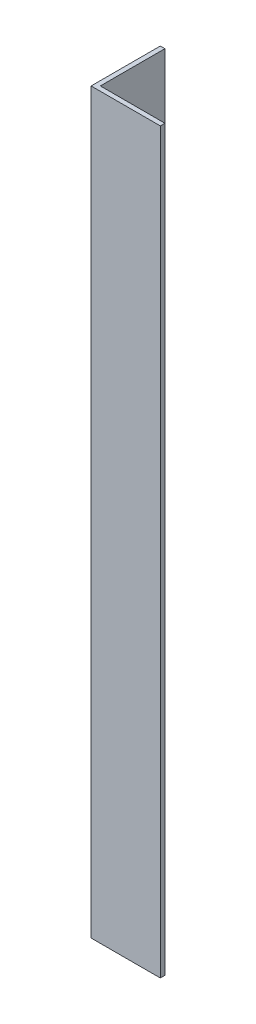
SolidWorks part; units mm, degrees
material "1060 Сплав"
ref_plane "Спереди" through (0, 0, 0) normal (0, 0, 1) x (1, 0, 0)
ref_plane "Сверху" through (0, 0, 0) normal (0, 1, 0) x (1, 0, 0)
ref_plane "Справа" through (0, 0, 0) normal (1, 0, 0) x (0, 0, -1)
sketch "Эскиз1" plane through (0, 0, 0) normal (0, 1, 0) x (1, 0, 0)
  line L0 (0, 0) -> (0, 15)
  line L1 (0, 15) -> (1, 15)
  line L2 (1, 15) -> (1, 1)
  line L3 (1, 1) -> (15, 1)
  line L4 (15, 1) -> (15, 0)
  line L5 (15, 0) -> (0, 0)
  dimension "D1" = 1
  dimension "D2" = 15
extrude "Бобышка-Вытянуть1" add sketch "Эскиз1" along normal blind 160
